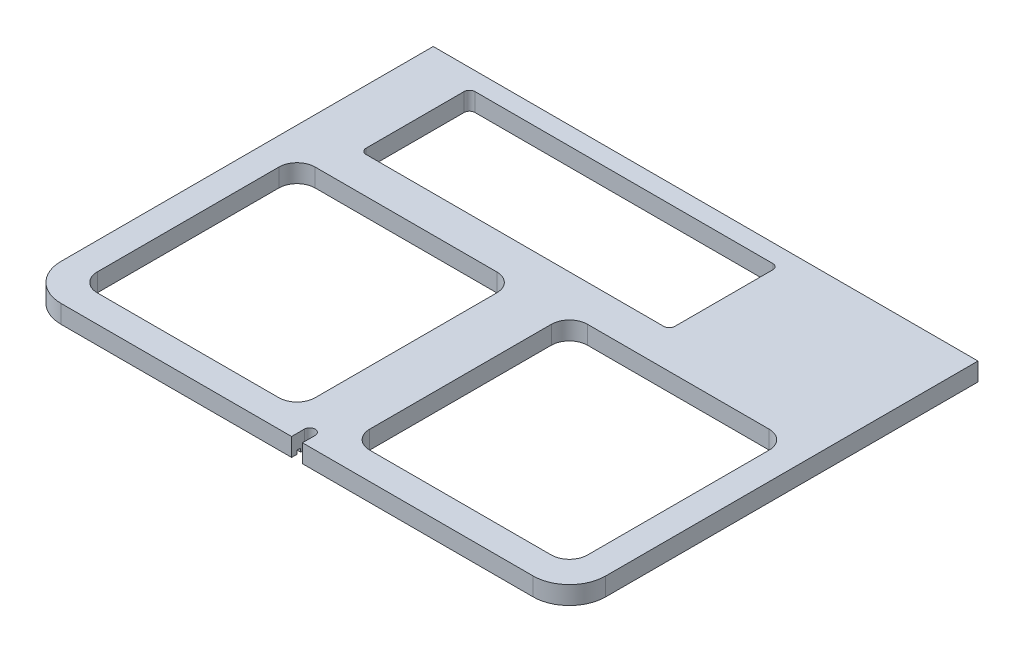
SolidWorks part; units mm, degrees
ref_plane "Ebene vorne" through (0, 0, 0) normal (0, 0, 1) x (1, 0, 0)
ref_plane "Ebene oben" through (0, 0, 0) normal (0, 1, 0) x (1, 0, 0)
ref_plane "Ebene rechts" through (0, 0, 0) normal (1, 0, 0) x (0, 0, -1)
sketch "Skizze1" plane through (0, 10, 0) normal (0, 1, 0) x (1, 0, 0)
  line L0 (0, -75) -> (130, -75)
  line L2 (0, -75) -> (0, 75)
  line L3 (0, 75) -> (150, 75) construction
  line L4 (150, -55) -> (150, 75)
  line L5 (150, -55) -> (150, 150) construction
  line L6 (15, -60) -> (15, -75) construction
  line L7 (15, 60) -> (135, 60)
  line L8 (15, 60) -> (15, -60)
  line L9 (15, -60) -> (135, -60)
  line L10 (135, 60) -> (135, -60)
  line L11 (15, -75) -> (15, -60) construction
  line L12 (0, -60) -> (15, -60) construction
  line L13 (135, 60) -> (135, 75) construction
  line L14 (135, 60) -> (150, 60) construction
  line L15 (150, 75) -> (150, 150)
  line L16 (150, 150) -> (0, 150)
  line L17 (0, 150) -> (0, 75)
  arc A0 (130, -75) -> (150, -55) centre (130, -55) ccw
  arc A1 (130, -75) -> (150, -55) centre (130, -55) ccw construction
  dimension "D1" = 120
  dimension "D2" = 150
extrude "Linear austragen1" add sketch "Skizze1" along normal blind 10
fillet "Verrundung2" radius 10 4 edges at (15, 15, 60) (135, 15, 60) (135, 15, -60) (15, 15, -60)
mirror "Spiegeln1" about plane through (0, 20, -150) normal (1, 0, 0) of "Verrundung2", "Linear austragen1"
sketch "Skizze3" plane through (0, 10, 0) normal (0, -1, 0) x (1, 0, 0)
  line L0 (-150, 55) -> (-150, -150) construction
  line L1 (-120, -80) -> (50, -80)
  line L2 (-120, -80) -> (-120, -140)
  line L3 (-120, -140) -> (50, -140)
  line L4 (50, -80) -> (50, -140)
  line L5 (150, -150) -> (-150, -150) construction
  line L6 (0, -60.4164) -> (0, -150) construction
  dimension "D1" = 30
  dimension "D2" = 10
  dimension "D3" = 50
  dimension "D4" = 60
extrude "Schnitt-Linear austragen1" cut sketch "Skizze3" against normal blind 10
fillet "Verrundung3" radius 3 4 edges at (-120, 15, -140) (50, 15, -140) (50, 15, -80) (-120, 15, -80)
sketch "Skizze4" plane through (0, 10, 0) normal (0, -1, 0) x (1, 0, 0)
  line L0 (-3.0001, 75) -> (-3.0001, 68)
  line L1 (-130, 75) -> (130, 75) construction
  line L2 (-3.0001, 75) -> (2.9592, 75)
  line L3 (2.9592, 75) -> (2.9999, 68.0175)
  arc A0 (-3.0001, 68) -> (2.9999, 68.0175) centre (-0.0001, 68) ccw
  dimension "D2" = 3
  dimension "D1" = 7
extrude "Schnitt-Linear austragen2" cut sketch "Skizze4" against normal blind 10
sketch "Skizze5" plane through (0, 10, 0) normal (0, -1, 0) x (1, 0, 0)
  line L0 (-7.0204, 72) -> (-3.0001, 75) construction
  line L1 (-7.0204, 72) -> (6.9796, 72)
  line L2 (-7.0204, 72) -> (-7.0204, 70)
  line L3 (-7.0204, 70) -> (6.9796, 70)
  line L4 (6.9796, 72) -> (6.9796, 70)
  line L5 (2.9592, 75) -> (6.9796, 72) construction
  dimension "D1" = 14
  dimension "D2" = 2
  dimension "D3" = 3
extrude "Schnitt-Linear austragen3" cut sketch "Skizze5" against normal blind 2
